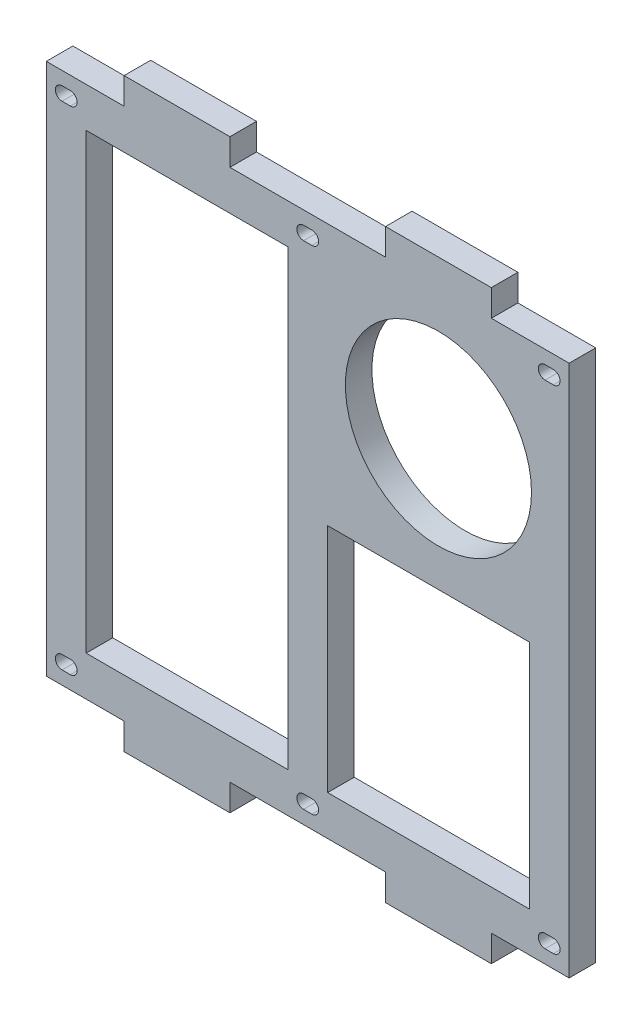
SolidWorks part; units mm, degrees
ref_plane "Alzado" through (0, 0, 0) normal (0, 0, 1) x (1, 0, 0)
ref_plane "Planta" through (0, 0, 0) normal (0, 1, 0) x (1, 0, 0)
ref_plane "Vista lateral" through (0, 0, 0) normal (1, 0, 0) x (0, 0, -1)
sketch "Croquis1" plane through (0, 0, 0) normal (0, 0, 1) x (1, 0, 0)
  line L0 (62.5, 140) -> (62.5, -140) construction
  line L1 (-125, -140) -> (125, -140)
  line L2 (-125, -140) -> (-125, 140)
  line L3 (-125, 140) -> (125, 140)
  line L4 (125, -140) -> (125, 140)
  line L5 (-125, -140) -> (125, 140) construction
  line L6 (-125, 140) -> (125, -140) construction
  line L7 (-105.95, 108.25) -> (-9.525, 108.25)
  line L8 (-105.95, 108.25) -> (-105.95, -108.25)
  line L9 (-105.95, -108.25) -> (-9.525, -108.25)
  line L10 (-9.525, 108.25) -> (-9.525, -108.25)
  line L11 (9.525, 2.3) -> (105.95, 2.3)
  line L12 (9.525, 2.3) -> (9.525, -108.25)
  line L13 (9.525, -108.25) -> (105.95, -108.25)
  line L14 (105.95, 2.3) -> (105.95, -108.25)
  line L15 (-9.525, -108.25) -> (9.525, -108.25) construction
  circle A0 centre (62.5, 64.8) radius 44.5
  point P0 (0, 0)
  point P18 (0, -108.25)
  dimension "D4" = 89
  dimension "D5" = 75.2
  dimension "D13" = 62.5
  dimension "D1" = 280
  dimension "D2" = 250
  dimension "D3" = 62.5
  dimension "D6" = 31.75
  dimension "D7" = 31.75
  dimension "D8" = 31.75
  dimension "D9" = 19.05
  dimension "D10" = 19.05
  dimension "D11" = 19.05
  dimension "D12" = 125
extrude "Saliente-Extruir1" add sketch "Croquis1" along normal blind 12.7 contours L3 L4 L1 L2
sketch "Croquis2" plane through (0, 0, 12.7) normal (0, 0, 1) x (1, 0, 0)
  line L0 (125, 140) -> (-125, 140) construction
  line L1 (-125, 140) -> (-87.8, 140)
  line L2 (-125, 140) -> (-125, 127.3)
  line L3 (-125, 127.3) -> (-87.8, 127.3)
  line L4 (-87.8, 140) -> (-87.8, 127.3)
  line L5 (-37.2, 140) -> (37.2, 140)
  line L6 (-37.2, 140) -> (-37.2, 127.3)
  line L7 (-37.2, 127.3) -> (37.2, 127.3)
  line L8 (37.2, 140) -> (37.2, 127.3)
  line L9 (125, -140) -> (125, 140) construction
  line L10 (87.8, 140) -> (125, 140)
  line L11 (87.8, 140) -> (87.8, 127.3)
  line L12 (87.8, 127.3) -> (125, 127.3)
  line L13 (125, 140) -> (125, 127.3)
  line L14 (-115.475, 127.3) -> (-115.475, 113.5153) construction
  line L15 (0, 127.3) -> (0, 113.5153) construction
  line L16 (115.475, 127.3) -> (115.475, 113.5153) construction
  line L17 (-125, 140) -> (-125, -140) construction
  line L22 (-117.475, 117.75) -> (-113.475, 117.75) construction
  line L23 (-117.475, 120.95) -> (-113.475, 120.95)
  line L24 (-117.475, 114.55) -> (-113.475, 114.55)
  line L25 (-2, 117.75) -> (2, 117.75) construction
  line L26 (-2, 120.95) -> (2, 120.95)
  line L27 (-2, 114.55) -> (2, 114.55)
  line L28 (113.475, 117.75) -> (117.475, 117.75) construction
  line L29 (113.475, 120.95) -> (117.475, 120.95)
  line L30 (113.475, 114.55) -> (117.475, 114.55)
  arc A0 (-117.475, 120.95) -> (-117.475, 114.55) centre (-117.475, 117.75) ccw
  arc A1 (-113.475, 114.55) -> (-113.475, 120.95) centre (-113.475, 117.75) ccw
  arc A2 (-2, 120.95) -> (-2, 114.55) centre (-2, 117.75) ccw
  arc A3 (2, 114.55) -> (2, 120.95) centre (2, 117.75) ccw
  arc A4 (113.475, 120.95) -> (113.475, 114.55) centre (113.475, 117.75) ccw
  arc A5 (117.475, 114.55) -> (117.475, 120.95) centre (117.475, 117.75) ccw
  point P27 (-115.475, 117.75)
  point P36 (0, 117.75)
  point P42 (115.475, 117.75)
  dimension "D8" = 3.2
  dimension "D10" = 4
  dimension "D11" = 3.2
  dimension "D13" = 3.2
  dimension "D1" = 12.7
  dimension "D2" = 50.6
  dimension "D3" = 50.6
  dimension "D4" = 37.2
  dimension "D5" = 37.2
  dimension "D6" = 9.525
  dimension "D7" = 9.525
  dimension "D9" = 6.35
  dimension "D12" = 4
  dimension "D14" = 4
extrude "Cortar-Extruir1" cut sketch "Croquis2" against normal through all
mirror "Simetría1" about plane through (0, 0, 0) normal (0, 1, 0) of "Cortar-Extruir1"
